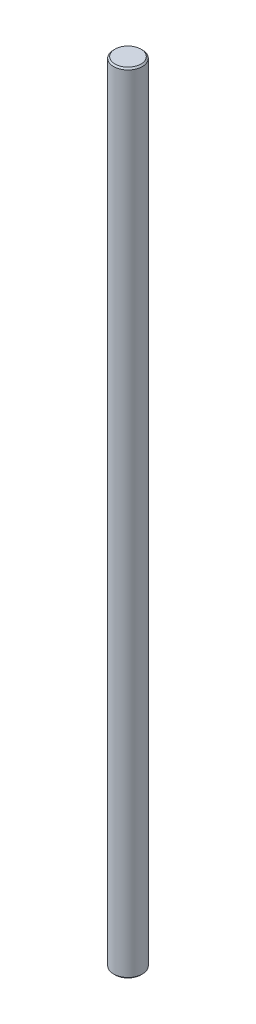
SolidWorks part; units mm, degrees
ref_plane "Front Plane" through (0, 0, 0) normal (0, 0, 1) x (1, 0, 0)
ref_plane "Top Plane" through (0, 0, 0) normal (0, 1, 0) x (1, 0, 0)
ref_plane "Right Plane" through (0, 0, 0) normal (1, 0, 0) x (0, 0, -1)
sketch "MainSketch" plane through (0, 0, 0) normal (0, 1, 0) x (1, 0, 0)
  circle A0 centre (0, 0) radius 5
  dimension "D1" = 10
extrude "Boss-Extrude1" add sketch "MainSketch" along normal blind 100 and the other way blind 174.3074
chamfer "Chamfer1" distance 0.5 angle 45 2 edges at (0, 100, 5) (0, -174.3074, 5)
